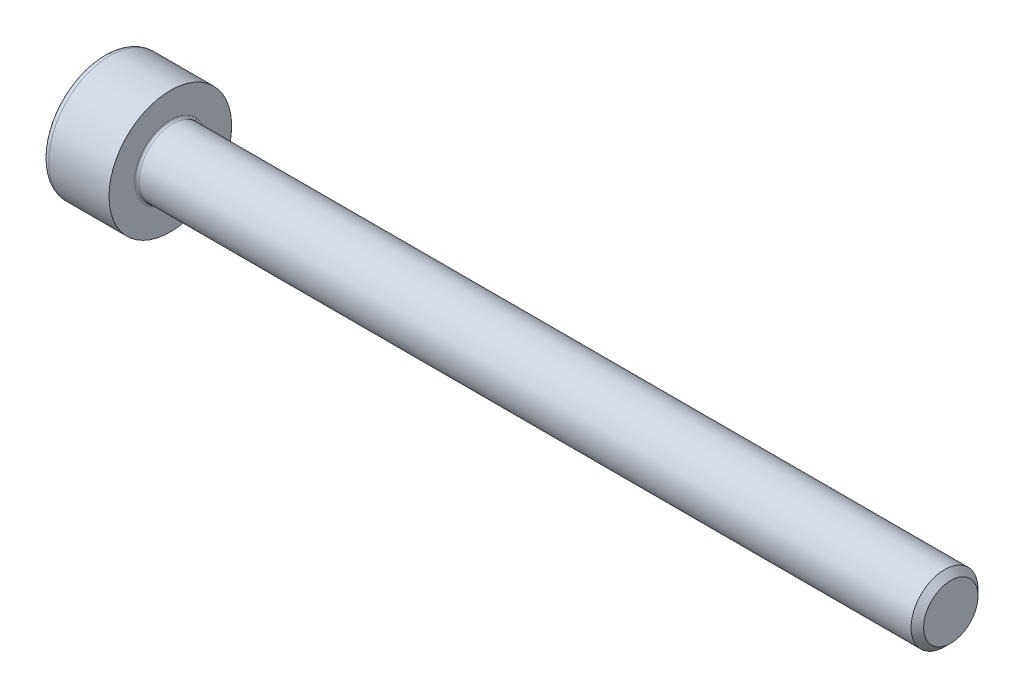
SolidWorks part; units mm, degrees
revolve "Base-Revolve" add sketch "BodySke"
sketch "BodySke" plane through (0, 0, 0) normal (0, 0, 1) x (1, 0, 0)
  line L0 (0, 0) -> (0, 2.75)
  line L1 (0, 2.75) -> (3, 2.75)
  line L2 (3, 2.75) -> (3, 1.5)
  line L3 (3, 1.5) -> (37.7195, 1.5)
  line L4 (38, 1.2195) -> (38, 0)
  line L5 (38, 0) -> (0, 0)
  line L6 (-31.75, 0) -> (127, 0) construction
  line L8 (38, 1.2195) -> (37.7195, 1.5)
  line L10 (38, -1.2195) -> (37.7195, -1.5) construction
  line L11 (3.5, 9.525) -> (3.5, 3.175) construction
  line L12 (33, 9.525) -> (33, 3.175) construction
  line L13 (-22, 9.525) -> (-22, 3.175) construction
  dimension "Head_ht" = 3
  dimension "Length" = 35
  dimension "Body_ch_ang" = 45
  dimension "Diameter" = 3
  dimension "Minor_dia" = 2.439
  dimension "Advance" = 0.5
  dimension "Thread_nom" = 5
  dimension "Thread_length" = 60
  dimension "Head_dia" = 5.5
cosmetic thread "ThreadCosmetic" [suppressed]
fillet "Fillet1" radius 0.1 1 edges at (3, 0, 1.5)
fillet "Fillet2" radius 0.3 1 edges at (0, 0, 2.75)
ref_plane "Plane1" through (0, 0, 0) normal (0, 0, 1) x (1, 0, 0)
ref_plane "Plane2" through (0, 0, 0) normal (0, 1, 0) x (1, 0, 0)
ref_plane "Plane3" through (0, 0, 0) normal (1, 0, 0) x (0, 0, -1)
other "Configuration Table"
sketch "Sketch2" plane through (0, 0, 0) normal (0, 0, 1) x (1, 0, 0)
  line L0 (0, 1.26) -> (1.3, 1.26)
  line L1 (1.3, 1.26) -> (2.0275, 0)
  line L2 (-31.75, 0) -> (127, 0) construction
  line L3 (2.0275, 0) -> (0, 0)
  line L4 (0, 0) -> (0, 1.26)
  line L6 (0, 0) -> (47.625, 0) construction
  dimension "D1" = 1.26
  dimension "D2" = 60
  dimension "Depth" = 1.3
revolve "Hex-PreBroach" cut sketch "Sketch2" angle 360 about L6
sketch "Sketch3" plane through (0, 0, 0) normal (-1, 0, 0) x (0, 0.5, 0.866)
  line L0 (0.7275, 1.26) -> (-0.7275, 1.26)
  line L1 (-0.7275, 1.26) -> (-1.4549, 0)
  line L2 (0.7275, 1.26) -> (1.4549, 0)
  line L3 (0.7275, -1.26) -> (1.4549, 0)
  line L4 (0.7275, -1.26) -> (-0.7275, -1.26)
  line L5 (-0.7275, -1.26) -> (-1.4549, 0)
  dimension "D1" = 1.26
  dimension "D2" = 1.26
  dimension "Hex_size" = 2.52
extrude "Hex" cut sketch "Sketch3" against normal blind 1.3
sketch "ThdSchSke" plane through (0, 0, 0) normal (0, 0, 1) x (1, 0, 0)
  line L0 (33, -1.2195) -> (32.8036, -1.5)
  line L1 (33, -1.2195) -> (33.1964, -1.5)
  line L2 (33.1964, -1.5) -> (33.1964, -1.875)
  line L3 (-3.175, 0) -> (5.1513, 0) construction
  line L4 (0, 2.45) -> (0, -2.45) construction
  line L5 (33.1964, -1.875) -> (32.8036, -1.875)
  line L6 (32.8036, -1.875) -> (32.8036, -1.5)
  dimension "Thread_minor" = 2.439
  dimension "Diameter" = 3
  dimension "Start" = 33
revolve "ThreadSchematic" [suppressed] cut sketch "ThdSchSke" angle 360 about L3
pattern_linear "ThdSchPat" [suppressed]
equation "\"D2@Sketch3\" = \"Hex_size@Sketch3\" / 2"
equation "\"D1@Sketch3\" = \"Hex_size@Sketch3\" / 2"
equation "\"D1@Sketch2\" = \"Hex_size@Sketch3\" / 2"
equation "\"Thread_minor@ThreadCosmetic\"  =  \"Minor_dia@BodySke\""
equation "\"Depth@Sketch2\" =  \"Key_eng@Hex\""
equation "\"Thread_length@ThreadCosmetic\" = ((sgn( (\"Length@BodySke\" - \"Advance@BodySke\" * 3.0) - \"Thread_nom@BodySke\" )-1)*( (\"Length@BodySke\" - \"Advance@BodySke\" * 3.0) - \"Thread_nom@BodySke\" ))/-2+ \"Thread_nom@BodySke\""
equation "\"Thread_minor@ThdSchSke\" = \"Minor_dia@BodySke\""
equation "\"Diameter@ThdSchSke\" = \"Diameter@BodySke\""
equation "\"Overcut@ThdSchSke\" = \"Diameter@BodySke\" * 1.25"
equation "\"Start@ThdSchSke\" = \"Head_ht@BodySke\" + \"Length@BodySke\" - \"Thread_length@ThreadCosmetic\"  '---Non-countersunk---"
equation "\"Num_threads@ThdSchPat\" = int( \"Thread_length@ThreadCosmetic\" / \"Advance@BodySke\" + 0.999 )  + 1"
equation "\"Advance@ThdSchPat\" = \"Thread_length@ThreadCosmetic\" /  (\"Num_threads@ThdSchPat\" - 1) 'relax it"
equation "\"Num_threads@ThdSchPat\" = \"Num_threads@ThdSchPat\" - sgn( \"Num_threads@ThdSchPat\" - 1) '---chamfered tips only---"
